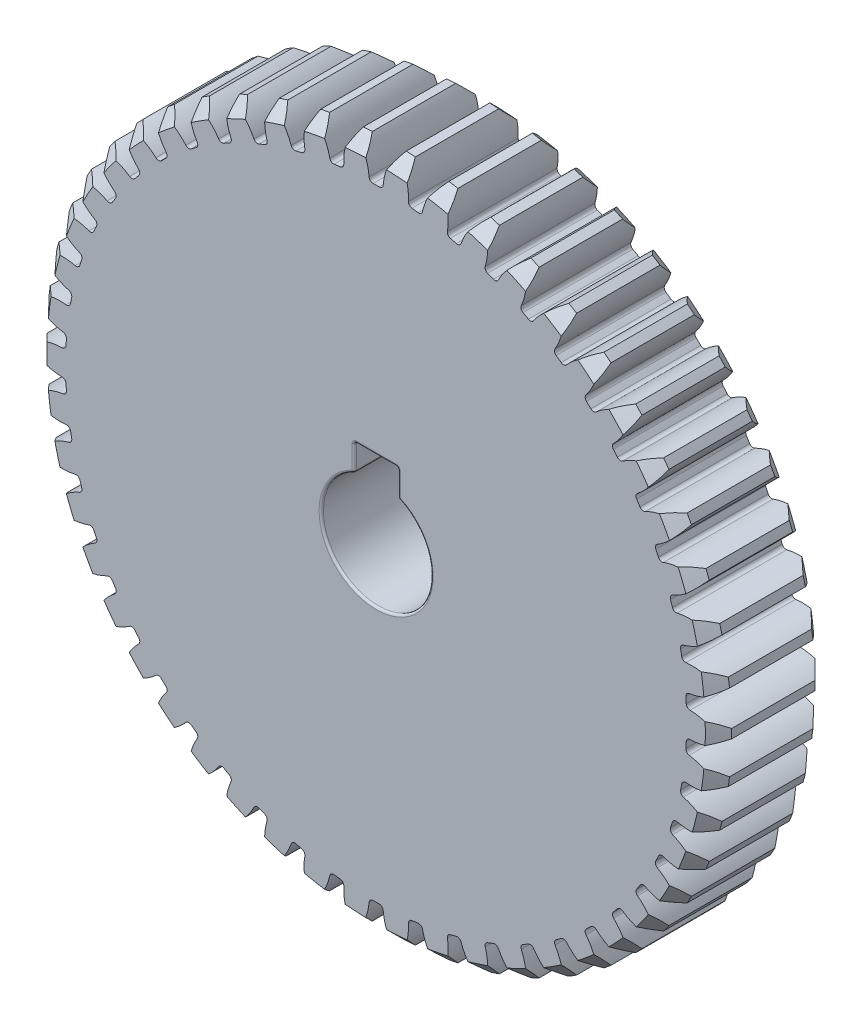
SolidWorks part; units mm, degrees
ref_plane "Front Plane" through (0, 0, 0) normal (0, 0, 1) x (1, 0, 0)
ref_plane "Top Plane" through (0, 0, 0) normal (0, 1, 0) x (1, 0, 0)
ref_plane "Right Plane" through (0, 0, 0) normal (1, 0, 0) x (0, 0, -1)
sketch "Sketch1" plane through (0, 0, 0) normal (0, 0, 1) x (1, 0, 0)
  circle A0 centre (0, 0) radius 30 construction
  circle A1 centre (0, 0) radius 31.2
  dimension "D1" = 60
  dimension "D2" = 62.4
extrude "Boss-Extrude1" add sketch "Sketch1" along normal mid plane 10
sketch "Sketch2" plane through (0, 0, 0) normal (0, 0, 1) x (1, 0, 0)
  line L0 (0, 0) -> (0, 31.2) construction
  line L1 (0, 0) -> (3.9104, 30.954) construction
  line L2 (0, 0) -> (1.9591, 31.1384) construction
  line L3 (-0.6247, 28.2931) -> (0, 0) construction
  line L4 (-0.9423, 29.9852) -> (0.9423, 29.9852) construction
  line L5 (0.9423, 29.9852) -> (2.8232, 29.8669) construction
  line L6 (-1.3735, 31.1698) -> (0, 27.3962) construction
  circle A0 centre (0, 0) radius 28.8 construction
  circle A2 centre (0, 0) radius 31.2 construction
  arc A3 (-1.5465, 31.1616) -> (-0.6247, 28.2931) centre (-5.912, 28.1764) cw
  circle A4 centre (0, 0) radius 31.2 construction
  arc A5 (1.5465, 31.1616) -> (0.6247, 28.2931) centre (5.912, 28.1764) ccw
  circle A6 centre (0, 0) radius 30 construction
  arc A7 (0.6247, 28.2931) -> (-0.6247, 28.2931) centre (0, 0) ccw
  arc A8 (1.5465, 31.1616) -> (-1.5465, 31.1616) centre (0, 0) ccw
  dimension "D1" = 7.2
  dimension "D2" = 2.4
  dimension "D4" = 20
  dimension "D3" = 0.5
extrude "Cut-Extrude1" cut sketch "Sketch2" against normal through all both and the other way through all contours A5 A8 A3 A7
fillet "Fillet1" radius 0.36 2 edges at (0.6247, 28.2931, 0) (-0.6247, 28.2931, 0)
chamfer "Chamfer1" distance 1.2 angle 45 2 edges at (0, -31.2, -5) (0, -31.2, 5)
pattern_circular "CirPattern1" count 50 over 360 about axis through (0, 0, 0) along (0, 0, 1) of "Fillet1", "Cut-Extrude1"
sketch "Sketch3" plane through (0, 0, 5) normal (0, 0, 1) x (1, 0, 0)
  line L2 (-2, 4.5826) -> (-2, 7)
  line L3 (-2, 7) -> (2, 7)
  line L4 (2, 4.5826) -> (2, 7)
  arc A0 (-2, 4.5826) -> (2, 4.5826) centre (0, 0) ccw
  point P3 (0, 5)
  point P5 (0, 7)
  dimension "D1" = 10
  dimension "D2" = 2
  dimension "D3" = 4
extrude "Cut-Extrude2" cut sketch "Sketch3" against normal through all
fillet "Fillet2" radius 0.2 12 edges at (0, -5, 5) (0, -5, -5) (-2, 4.5826, 0) (2, 4.5826, 0) (0, 7, -5) (0, 7, 5) (-2, 7, 0) (-2, 5.7913, -5) (-2, 5.7913, 5) (2, 5.7913, -5) (2, 7, 0) (2, 5.7913, 5)
sketch "Sketch4" plane through (0, 0, 0) normal (0, 0, 1) x (1, 0, 0)
  circle A0 centre (0, 0) radius 30
equation "\"Module\"= 1.2"
equation "\"Number of Teeth\"= 50'Number of Teeth"
equation "\"Pressure Angle\"= 20"
equation "\"D1@Sketch1\"=\"Module\" * \"Number of Teeth\""
equation "\"D2@Sketch1\"=( \"Number of Teeth\" + 2) * \"Module\""
equation "\"D1@Sketch2\"=360 / \"Number of Teeth\""
equation "\"D2@Sketch2\"= \"Module\" * 2"
equation "\"D4@Sketch2\"=\"Pressure Angle\""
equation "\"D1@Fillet1\"=0.3 * \"Module\""
equation "\"D1@CirPattern1\"= \"Number of Teeth\""
equation "\"D1@Chamfer1\"= \"Module\""
equation "\"Gear Thickness\"= 10"
equation "\"D1@Boss-Extrude1\"= \"Gear Thickness\""
